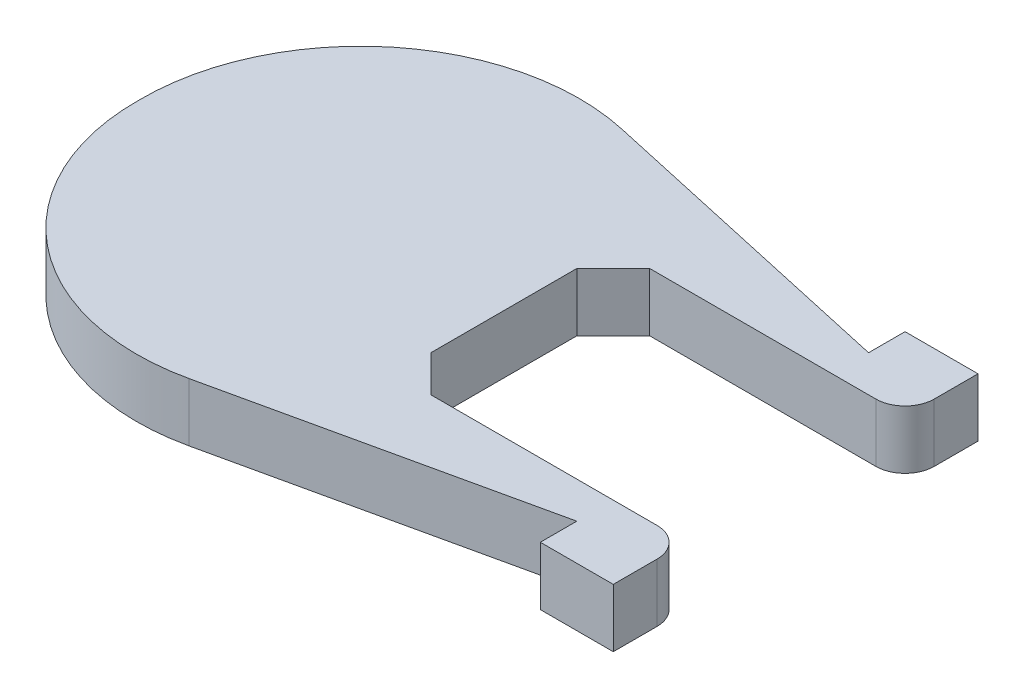
SolidWorks part; units mm, degrees
ref_plane "Přední rovina" through (0, 0, 0) normal (0, 0, 1) x (1, 0, 0)
ref_plane "Vrchní rovina" through (0, 0, 0) normal (0, 1, 0) x (1, 0, 0)
ref_plane "Pravá rovina" through (0, 0, 0) normal (1, 0, 0) x (0, 0, -1)
sketch "Skica1" plane through (0, 0, 0) normal (0, 1, 0) x (1, 0, 0)
  line L0 (0, -10) -> (0, 10)
  line L1 (5, 15) -> (36, 15)
  line L2 (40, 19) -> (40, 25)
  line L3 (40, 25) -> (30, 25)
  line L4 (30, 25) -> (30, 20)
  line L5 (30, 20) -> (-13.5068, 29.6452)
  line L6 (59.4942, 0) -> (-122.0755, 0) construction
  line L7 (0, 10) -> (5, 15)
  line L8 (0, -10) -> (5, -15)
  line L9 (30, -20) -> (-13.5068, -29.6452)
  line L10 (30, -25) -> (30, -20)
  line L11 (40, -25) -> (30, -25)
  line L12 (40, -19) -> (40, -25)
  line L13 (5, -15) -> (36, -15)
  arc A0 (-13.5068, 29.6452) -> (-49.9979, 0) centre (-20, 0.3563) ccw
  arc A1 (36, 15) -> (40, 19) centre (36, 19) ccw
  arc A2 (36, -15) -> (40, -19) centre (36, -19) cw
  arc A3 (-13.5068, -29.6452) -> (-49.9979, 0) centre (-20, -0.3563) cw
  point P0 (59.4942, 0)
  point P1 (0, 15)
  point P12 (-13.7611, 29.3041)
  point P22 (0, -15)
  point P28 (0, 0)
  dimension "D6" = 30
  dimension "D9" = 4
  dimension "D1" = 40
  dimension "D2" = 10
  dimension "D3" = 30
  dimension "D4" = 40
  dimension "D5" = 50
  dimension "D7" = 60
  dimension "D8" = 12.5
extrude "Přidat vysunutím2" add sketch "Skica1" along normal blind 8
